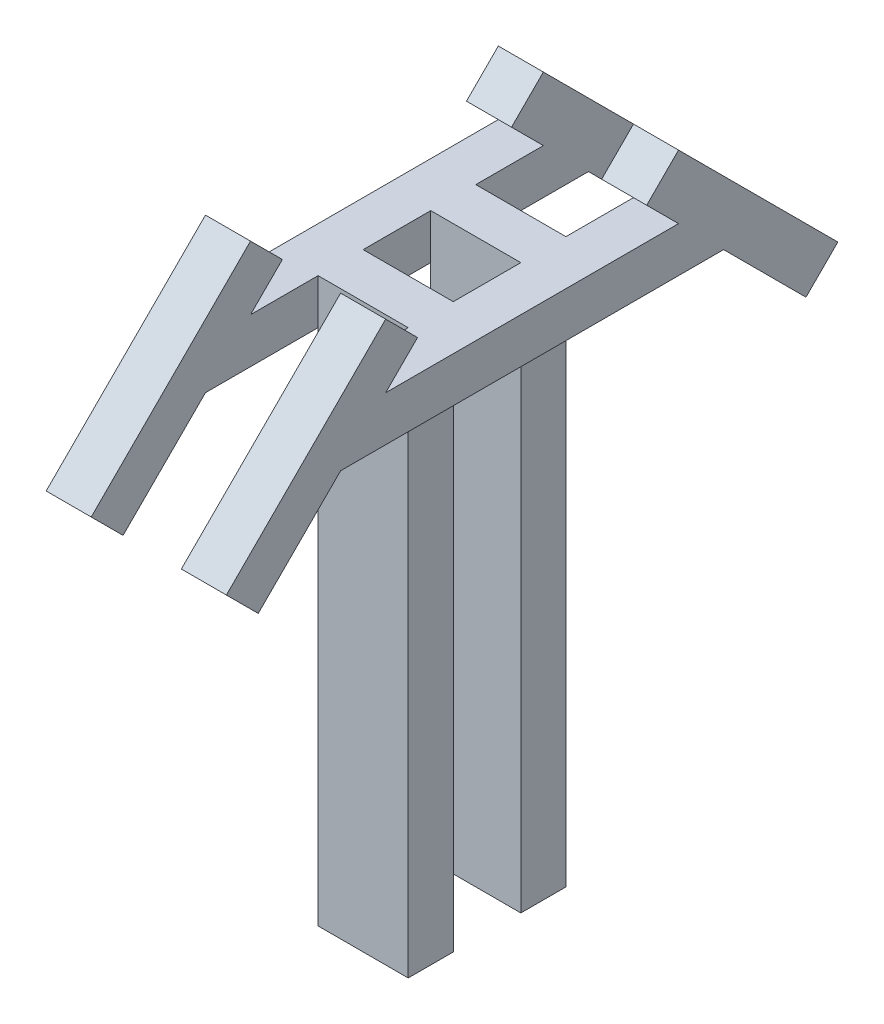
SolidWorks part; units mm, degrees
ref_plane "前视基准面" through (0, 0, 0) normal (0, 0, 1) x (1, 0, 0)
ref_plane "上视基准面" through (0, 0, 0) normal (0, 1, 0) x (1, 0, 0)
ref_plane "右视基准面" through (0, 0, 0) normal (1, 0, 0) x (0, 0, -1)
sketch "草图1" plane through (0, 0, 0) normal (0, 1, 0) x (1, 0, 0)
  line L1 (0, 0) -> (80, 0)
  line L2 (0, 0) -> (0, -40)
  line L3 (0, -40) -> (80, -40)
  line L4 (80, 0) -> (80, -40)
  line L5 (0, 100) -> (80, 100)
  line L6 (0, 100) -> (0, 60)
  line L7 (0, 60) -> (80, 60)
  line L8 (80, 100) -> (80, 60)
  point P9 (0, 80)
  point P10 (0, -20)
  dimension "D1" = 80
  dimension "D2" = 40
  dimension "D3" = 40
  dimension "D4" = 100
extrude "凸台-拉伸1" add sketch "草图1" along normal blind 500
sketch "草图2" plane through (80, 0, 0) normal (1, 0, 0) x (0, 0, -1)
  line L0 (60, 500) -> (100, 500) construction
  line L1 (-140, 500) -> (200, 500)
  line L2 (-140, 500) -> (-140, 460)
  line L3 (-140, 460) -> (200, 460)
  line L4 (200, 500) -> (200, 460)
  line L5 (-40, 500) -> (-40, 0) construction
  line L6 (100, 500) -> (100, 0) construction
  dimension "D1" = 100
  dimension "D2" = 100
  dimension "D3" = 40
extrude "凸台-拉伸2" add sketch "草图2" along normal blind 40
sketch "草图3" plane through (0, 0, 0) normal (-1, 0, 0) x (0, 0, 1)
  line L0 (-100, 500) -> (-60, 500) construction
  line L1 (-200, 500) -> (140, 500)
  line L2 (-200, 500) -> (-200, 460)
  line L3 (-200, 460) -> (140, 460)
  line L4 (140, 500) -> (140, 460)
  line L5 (-100, 500) -> (-100, 0) construction
  line L6 (40, 500) -> (40, 0) construction
  dimension "D1" = 100
  dimension "D2" = 40
  dimension "D3" = 100
extrude "凸台-拉伸3" add sketch "草图3" along normal blind 40
sketch "草图4" plane through (-40, 0, 0) normal (-1, 0, 0) x (0, 0, 1)
  line L0 (140, 460) -> (100, 500)
  line L1 (140, 500) -> (-200, 500) construction
  line L2 (140, 460) -> (140, 500) construction
  line L3 (-200, 460) -> (-160, 500)
  line L4 (-200, 500) -> (-200, 460) construction
  line L5 (-160, 500) -> (-200, 500)
  line L6 (-200, 500) -> (-200, 460)
  line L7 (100, 500) -> (140, 500)
  line L8 (140, 500) -> (140, 460)
  dimension "D1" = 45
  dimension "D2" = 45
extrude "切除-拉伸1" cut sketch "草图4" against normal through all and the other way through all
sketch "草图5" plane through (0, 300, 300) normal (0, 0.7071, 0.7071) x (1, 0, 0)
  line L0 (-40, 282.8427) -> (-40, 466.6905) construction
  line L1 (-40, 322.8427) -> (0, 322.8427)
  line L2 (-40, 322.8427) -> (-40, 122.8427)
  line L3 (-40, 122.8427) -> (0, 122.8427)
  line L4 (0, 322.8427) -> (0, 122.8427)
  line L5 (0, 296.9848) -> (0, -28.2843) construction
  line L7 (80, 322.8427) -> (120, 322.8427)
  line L8 (80, 322.8427) -> (80, 122.8427)
  line L9 (80, 122.8427) -> (120, 122.8427)
  line L10 (120, 322.8427) -> (120, 122.8427)
  line L11 (0, 282.8427) -> (-40, 282.8427) construction
  line L13 (120, 282.8427) -> (80, 282.8427) construction
  point P14 (100, 122.8427)
  dimension "D1" = 200
  dimension "D2" = 40
  dimension "D3" = 200
  dimension "D4" = 40
  dimension "D5" = 40
extrude "凸台-拉伸4" add sketch "草图5" along normal blind 40
sketch "草图6" plane through (0, 330, -330) normal (0, 0.7071, -0.7071) x (1, 0, 0)
  line L0 (80, -240.4163) -> (80, -183.8478) construction
  line L1 (120, -280.4163) -> (80, -280.4163)
  line L2 (120, -280.4163) -> (120, -80.4163)
  line L3 (120, -80.4163) -> (80, -80.4163)
  line L4 (80, -280.4163) -> (80, -80.4163)
  line L5 (120, -183.8478) -> (120, -240.4163) construction
  line L6 (0, -183.8478) -> (0, -240.4163) construction
  line L7 (0, -280.4163) -> (-40, -280.4163)
  line L8 (0, -280.4163) -> (0, -80.4163)
  line L9 (0, -80.4163) -> (-40, -80.4163)
  line L10 (-40, -280.4163) -> (-40, -80.4163)
  line L11 (-40, -183.8478) -> (-40, -240.4163) construction
  line L12 (120, -240.4163) -> (80, -240.4163) construction
  line L13 (0, -240.4163) -> (-40, -240.4163) construction
  point P12 (-8.7558, -278.4066)
  dimension "D1" = 40
  dimension "D2" = 40
  dimension "D3" = 200
  dimension "D4" = 200
extrude "凸台-拉伸5" add sketch "草图6" along normal blind 40
